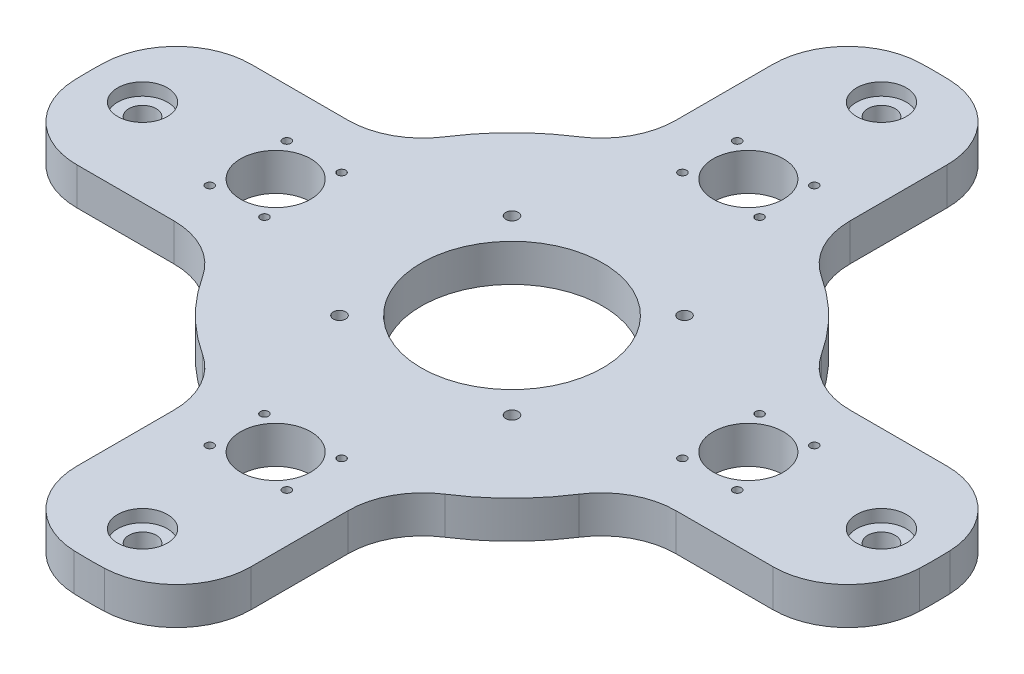
SolidWorks part; units mm, degrees
material "7075-T6, Plate (SS)"
ref_plane "Front Plane" through (0, 0, 0) normal (0, 0, 1) x (1, 0, 0)
ref_plane "Top Plane" through (0, 0, 0) normal (0, 1, 0) x (1, 0, 0)
ref_plane "Right Plane" through (0, 0, 0) normal (1, 0, 0) x (0, 0, -1)
sketch "Sketch1" plane through (0, 0, 0) normal (0, 1, 0) x (1, 0, 0)
  line L0 (-35, 166.358) -> (-35, 82.9156)
  line L1 (-34.67, -34.67) -> (34.67, -34.67) construction
  line L2 (-34.67, -34.67) -> (-34.67, 34.67) construction
  line L3 (-34.67, 34.67) -> (34.67, 34.67) construction
  line L4 (34.67, -34.67) -> (34.67, 34.67) construction
  line L5 (-34.67, -34.67) -> (34.67, 34.67) construction
  line L6 (-34.67, 34.67) -> (34.67, -34.67) construction
  line L7 (0, 0) -> (0, 170) construction
  line L8 (166.358, 35) -> (82.9156, 35)
  line L9 (35, 166.358) -> (35, 82.9156)
  line L10 (166.358, -35) -> (82.9156, -35)
  line L11 (35, -166.358) -> (35, -82.9156)
  line L12 (-35, -166.358) -> (-35, -82.9156)
  line L13 (-166.358, -35) -> (-82.9156, -35)
  line L14 (-166.358, 35) -> (-82.9156, 35)
  circle A0 centre (0, 0) radius 36.515
  circle A1 centre (0, 0) radius 170 construction
  arc A2 (-35, 82.9156) -> (-82.9156, 35) centre (0, 0) ccw
  circle A3 centre (0, 148.5) radius 10 construction
  arc A4 (35, 166.358) -> (-35, 166.358) centre (0, 0) ccw
  arc A5 (166.358, -35) -> (166.358, 35) centre (0, 0) ccw
  arc A6 (-35, -166.358) -> (35, -166.358) centre (0, 0) ccw
  arc A7 (35, -82.9156) -> (82.9156, -35) centre (0, 0) ccw
  arc A8 (82.9156, 35) -> (35, 82.9156) centre (0, 0) ccw
  arc A9 (-166.358, 35) -> (-166.358, -35) centre (0, 0) ccw
  arc A10 (-82.9156, -35) -> (-35, -82.9156) centre (0, 0) ccw
  point P26 (0, 0)
  dimension "D1" = 73.03
  dimension "D2" = 340
  dimension "D5" = 20
  dimension "D7" = 180
  dimension "D3" = 69.34
  dimension "D4" = 70
  dimension "D6" = 148.5
  dimension "D8" = 4
extrude "Boss-Extrude1" add sketch "Sketch1" along normal blind 15 contours L14 A9 L13 A2 | L8 A8 L9 A4 L0 A2 L12 A6 L11 A7 L10 A5 A0
fillet "Fillet1" radius 30 16 edges at (-35, 7.5, -82.9156) (-35, 7.5, -166.358) (35, 7.5, -166.358) (35, 7.5, -82.9156) (82.9156, 7.5, -35) (166.358, 7.5, -35) (166.358, 7.5, 35) (82.9156, 7.5, 35) (35, 7.5, 82.9156) (-35, 7.5, 166.358) (35, 7.5, 166.358) (-166.358, 7.5, 35) (-166.358, 7.5, -35) (-82.9156, 7.5, -35) (-35, 7.5, 82.9156) (-82.9156, 7.5, 35)
hole_wizard "M6 Tapped Hole1" positions "Sketch2" profile "Sketch3" tap size "M6" standard "ISO" end condition through all
sketch "Sketch2" plane through (0, 0, 0) normal (0, 1, 0) x (1, 0, 0)
  line L1 (-34.67, -34.67) -> (34.67, -34.67)
  line L2 (-34.67, -34.67) -> (-34.67, 34.67)
  line L3 (-34.67, 34.67) -> (34.67, 34.67)
  line L4 (34.67, -34.67) -> (34.67, 34.67)
  line L5 (-34.67, -34.67) -> (34.67, 34.67) construction
  line L6 (-34.67, 34.67) -> (34.67, -34.67) construction
  line L7 (-34.67, 0) -> (0, 0) construction
  line L8 (0, 0) -> (0, -34.67) construction
  point P13 (-34.67, 34.67)
  point P15 (34.67, 34.67)
  point P17 (34.67, -34.67)
  point P25 (-34.67, -34.67)
  dimension "D1" = 69.34
sketch "Sketch3" plane through (-34.67, 0, -34.67) normal (1, 0, 0) x (0, 0, -1)
  line L0 (0, 0) -> (0, 15)
  line L1 (0, 15) -> (2.5, 15)
  line L2 (2.5, 15) -> (2.5, 0)
  line L5 (2.5, 0) -> (0, 0)
  line L11 (0, -6.35) -> (0, 107.95) construction
  dimension "Thru Tap Drill Dia." = 5
  dimension "Thru Tap Drill Depth" = 15
cosmetic thread "Hole Thread21" parameters "D2"=6
cosmetic thread "Hole Thread22" parameters "D2"=6
cosmetic thread "Hole Thread23" parameters "D2"=6
cosmetic thread "Hole Thread24" parameters "D2"=6
sketch "Sketch4" plane through (0, 15, 0) normal (0, 1, 0) x (1, 0, 0)
  circle A0 centre (0, 148.5) radius 10 construction
  circle A1 centre (0, 148.5) radius 10
extrude "Cut-Extrude1" cut sketch "Sketch4" against normal blind 5
hole_wizard "M10 Clearance Hole1" positions "Sketch5" profile "Sketch6" hole size "M10" standard "ISO" end condition through all
sketch "Sketch5" plane through (0, 0, 0) normal (0, -1, 0) x (-1, 0, 0)
  point P0 (0, 148.5)
sketch "Sketch6" plane through (0, 0, -148.5) normal (1, 0, 0) x (0, 0, -1)
  line L0 (0, 0) -> (0, 15)
  line L1 (0, 15) -> (5.5, 15)
  line L2 (5.5, 15) -> (5.5, 0)
  line L5 (5.5, 0) -> (0, 0)
  line L11 (0, -6.35) -> (0, 107.95) construction
  dimension "Thru Hole Dia." = 11
  dimension "Thru Hole Depth" = 15
pattern_circular "CirPattern1" count 4 over 360 about axis through (0, 0, 0) along (0, 1, 0) of "M10 Clearance Hole1", "Cut-Extrude1"
sketch "Sketch7" plane through (0, 15, 0) normal (0, 1, 0) x (1, 0, 0)
  line L0 (0, 0) -> (0, 95) construction
  circle A0 centre (0, 95) radius 14.1
  dimension "D1" = 28.2
  dimension "D2" = 95
extrude "Cut-Extrude2" cut sketch "Sketch7" against normal through all
pattern_circular "CirPattern2" count 4 over 360 about axis through (0, 0, 0) along (0, 1, 0) of "Cut-Extrude2"
hole_wizard "M4 Tapped Hole1" positions "Sketch8" profile "Sketch9" tap size "M4" standard "ISO" end condition through all
sketch "Sketch8" plane through (0, 15, 0) normal (0, 1, 0) x (1, 0, 0)
  point P0 (-15.5, 106)
  point P3 (-15.5, 84)
  point P6 (15.5, 84)
  point P9 (15.5, 106)
sketch "Sketch9" plane through (-15.5, 15, -106) normal (1, 0, 0) x (0, 0, 1)
  line L0 (0, 0) -> (0, 15)
  line L1 (0, 15) -> (1.65, 15)
  line L2 (1.65, 15) -> (1.65, 0)
  line L5 (1.65, 0) -> (0, 0)
  line L11 (0, -6.35) -> (0, 107.95) construction
  dimension "Thru Tap Drill Dia." = 3.3
  dimension "Thru Tap Drill Depth" = 15
cosmetic thread "Hole Thread5" parameters "D2"=4
cosmetic thread "Hole Thread6" parameters "D2"=4
cosmetic thread "Hole Thread7" parameters "D2"=4
cosmetic thread "Hole Thread8" parameters "D2"=4
pattern_circular "CirPattern3" count 4 over 360 about axis through (0, 0, 0) along (0, 1, 0) of "M4 Tapped Hole1"
cosmetic thread "Hole Thread9" parameters "D2"=4
cosmetic thread "Hole Thread10" parameters "D2"=4
cosmetic thread "Hole Thread11" parameters "D2"=4
cosmetic thread "Hole Thread12" parameters "D2"=4
cosmetic thread "Hole Thread13" parameters "D2"=4
cosmetic thread "Hole Thread14" parameters "D2"=4
cosmetic thread "Hole Thread15" parameters "D2"=4
cosmetic thread "Hole Thread16" parameters "D2"=4
cosmetic thread "Hole Thread17" parameters "D2"=4
cosmetic thread "Hole Thread18" parameters "D2"=4
cosmetic thread "Hole Thread19" parameters "D2"=4
cosmetic thread "Hole Thread20" parameters "D2"=4
